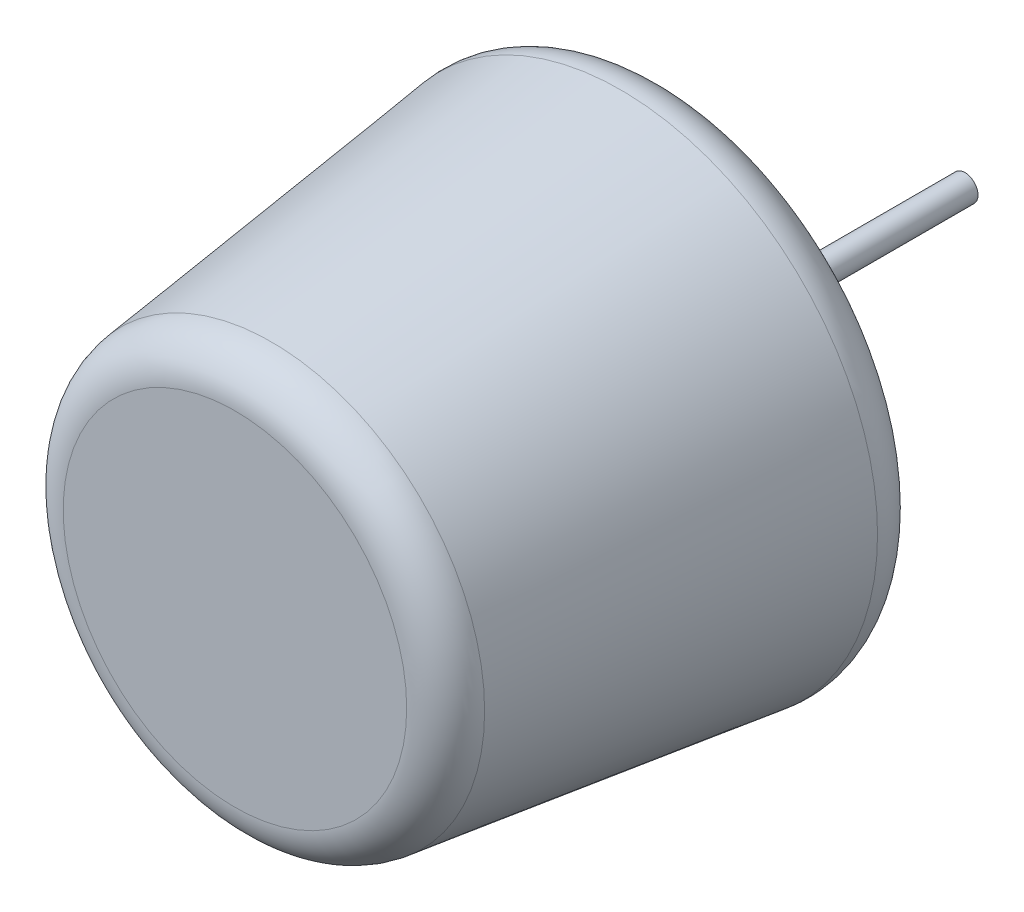
SolidWorks part; units mm, degrees
ref_plane "Front Plane" through (0, 0, 0) normal (0, 0, 1) x (1, 0, 0)
ref_plane "Top Plane" through (0, 0, 0) normal (0, 1, 0) x (1, 0, 0)
ref_plane "Right Plane" through (0, 0, 0) normal (1, 0, 0) x (0, 0, -1)
sketch "Sketch3" plane through (0, 0, 0) normal (0, 1, 0) x (1, 0, 0)
  line L0 (0, 0) -> (12.7, 0)
  line L1 (0, 0) -> (0, 25.4)
  line L3 (15.875, 25.4) -> (12.7, 0)
  line L4 (0, 25.4) -> (0, 31.75)
  line L7 (0.7937, 31.75) -> (15.875, 25.4)
  line L10 (0.7937, 31.75) -> (0.7937, 44.45)
  line L11 (0.7937, 44.45) -> (0, 44.45)
  line L12 (0, 31.75) -> (0, 44.45)
  dimension "D1" = 12.7
  dimension "D2" = 15.875
  dimension "D3" = 25.4
  dimension "D4" = 0.7937
  dimension "D5" = 6.35
  dimension "D6" = 12.7
revolve "Revolve1" add sketch "Sketch3" angle 360 about L1
fillet "Fillet1" radius 2.54 2 edges at (12.7, 0, 0) (15.875, 0, -25.4)
